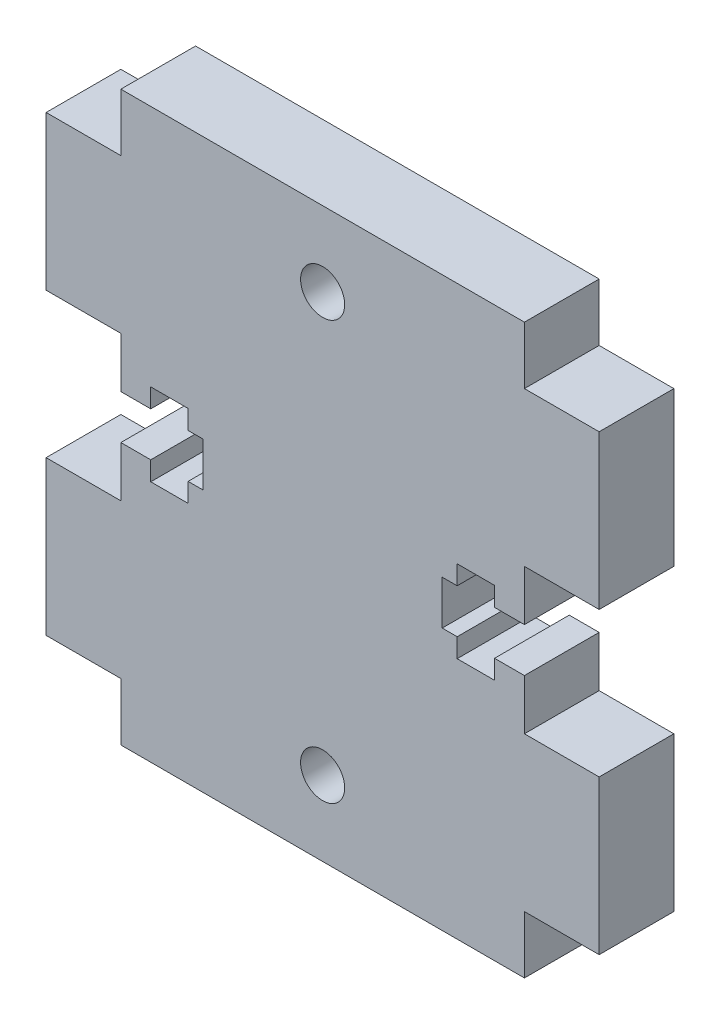
SolidWorks part; units mm, degrees
ref_plane "Front Plane" through (0, 0, 0) normal (0, 0, 1) x (1, 0, 0)
ref_plane "Top Plane" through (0, 0, 0) normal (0, 1, 0) x (1, 0, 0)
ref_plane "Right Plane" through (0, 0, 0) normal (1, 0, 0) x (0, 0, -1)
sketch "Sketch1" plane through (0, 0, 0) normal (0, 0, 1) x (1, 0, 0)
  line L0 (0, 0) -> (0, 15.5501) construction
  line L1 (0, 0) -> (20.3918, 0) construction
  line L2 (-13.5, 19) -> (13.5, 19)
  line L3 (13.5, 19) -> (13.5, 15.15)
  line L4 (13.5, 15.15) -> (18.5, 15.15)
  line L5 (18.5, 15.15) -> (18.5, 4.85)
  line L6 (18.5, 4.85) -> (13.5, 4.85)
  line L7 (13.5, 4.85) -> (13.5, 1.475)
  line L8 (13.5, 1.475) -> (11.5, 1.475)
  line L9 (11.5, 1.475) -> (11.5, 2.75)
  line L10 (11.5, 2.75) -> (9, 2.75)
  line L11 (9, 2.75) -> (9, 1.475)
  line L12 (9, 1.475) -> (8, 1.475)
  line L13 (8, 1.475) -> (8, -1.475)
  line L14 (-8, 1.475) -> (-8, -1.475)
  line L15 (-9, 1.475) -> (-8, 1.475)
  line L16 (-9, 2.75) -> (-9, 1.475)
  line L17 (-11.5, 2.75) -> (-9, 2.75)
  line L18 (-11.5, 1.475) -> (-11.5, 2.75)
  line L19 (-13.5, 1.475) -> (-11.5, 1.475)
  line L20 (-13.5, 4.85) -> (-13.5, 1.475)
  line L21 (-18.5, 4.85) -> (-13.5, 4.85)
  line L22 (-18.5, 15.15) -> (-18.5, 4.85)
  line L23 (-13.5, 15.15) -> (-18.5, 15.15)
  line L24 (-13.5, 19) -> (-13.5, 15.15)
  line L25 (-13.5, -19) -> (-13.5, -15.15)
  line L26 (-13.5, -15.15) -> (-18.5, -15.15)
  line L27 (-18.5, -15.15) -> (-18.5, -4.85)
  line L28 (-18.5, -4.85) -> (-13.5, -4.85)
  line L29 (-13.5, -4.85) -> (-13.5, -1.475)
  line L30 (-13.5, -1.475) -> (-11.5, -1.475)
  line L31 (-11.5, -1.475) -> (-11.5, -2.75)
  line L32 (-11.5, -2.75) -> (-9, -2.75)
  line L33 (-9, -2.75) -> (-9, -1.475)
  line L34 (-9, -1.475) -> (-8, -1.475)
  line L35 (9, -1.475) -> (8, -1.475)
  line L36 (9, -2.75) -> (9, -1.475)
  line L37 (11.5, -2.75) -> (9, -2.75)
  line L38 (11.5, -1.475) -> (11.5, -2.75)
  line L39 (13.5, -1.475) -> (11.5, -1.475)
  line L40 (13.5, -4.85) -> (13.5, -1.475)
  line L41 (18.5, -4.85) -> (13.5, -4.85)
  line L42 (18.5, -15.15) -> (18.5, -4.85)
  line L43 (13.5, -15.15) -> (18.5, -15.15)
  line L44 (13.5, -19) -> (13.5, -15.15)
  line L45 (-13.5, -19) -> (13.5, -19)
  circle A0 centre (0, 14) radius 1.475
  circle A1 centre (0, -14) radius 1.475
  point P29 (0, 19)
  point P40 (-8, 0)
  point P41 (8, 0)
  dimension "D13" = 2.95
  dimension "D1" = 13.5
  dimension "D2" = 3.85
  dimension "D3" = 19
  dimension "D4" = 5
  dimension "D5" = 10.3
  dimension "D6" = 3.375
  dimension "D7" = 2
  dimension "D8" = 1.275
  dimension "D9" = 2.5
  dimension "D10" = 5
  dimension "D11" = 1.275
  dimension "D12" = 1
  dimension "D14" = 14
extrude "Boss-Extrude1" add sketch "Sketch1" along normal blind 5
